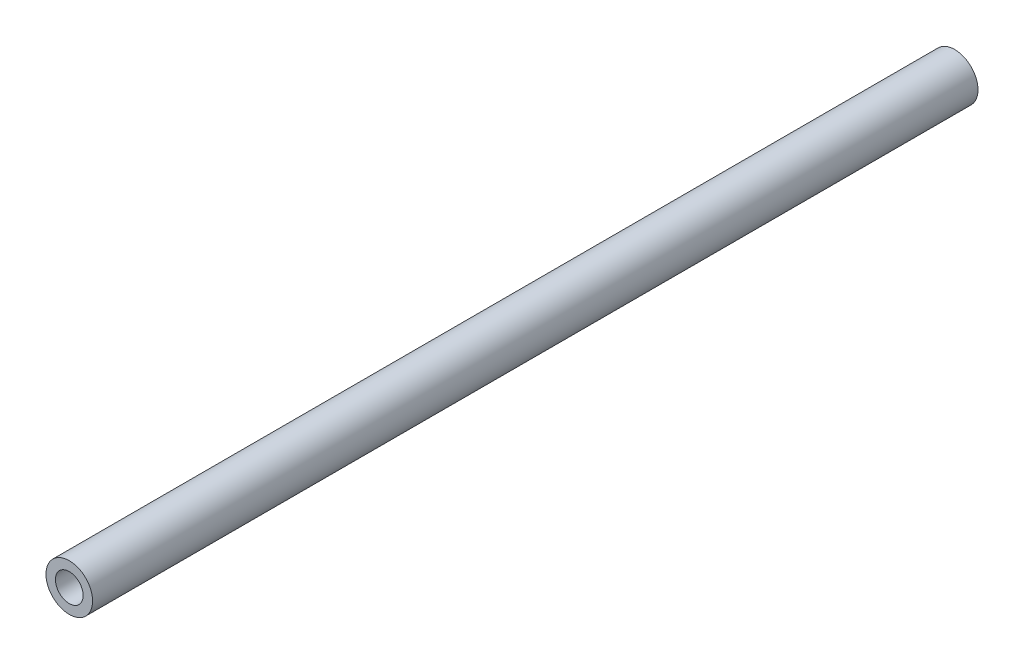
SolidWorks part; units mm, degrees
ref_plane "Front Plane" through (0, 0, 0) normal (0, 0, 1) x (1, 0, 0)
ref_plane "Top Plane" through (0, 0, 0) normal (0, 1, 0) x (1, 0, 0)
ref_plane "Right Plane" through (0, 0, 0) normal (1, 0, 0) x (0, 0, -1)
sketch "Sketch1" plane through (0, 0, 0) normal (0, 0, 1) x (1, 0, 0)
  circle A0 centre (0, 0) radius 7.9
  circle A1 centre (0, 0) radius 4.7
  dimension "D1" = 15.8
  dimension "D2" = 3.2
extrude "Boss-Extrude1" add sketch "Sketch1" along normal blind 300
